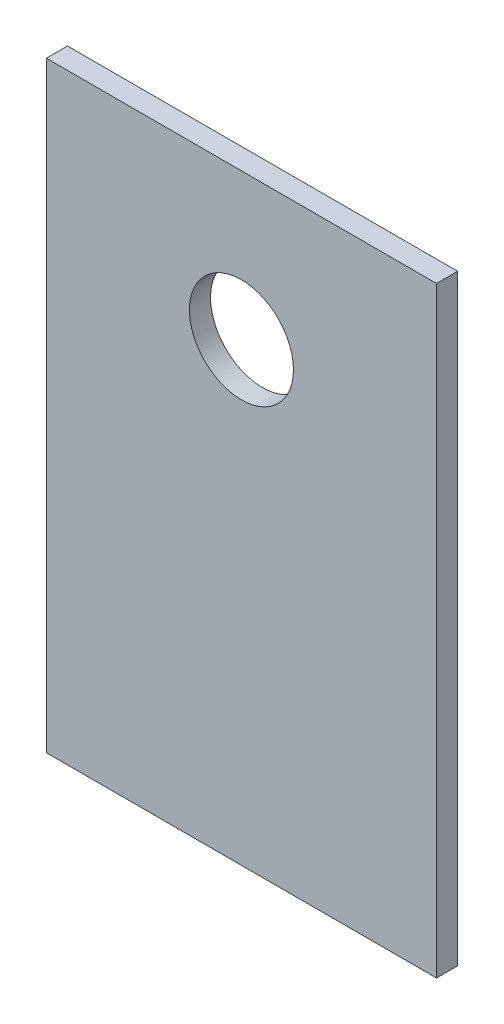
SolidWorks part; units mm, degrees
ref_plane "Front Plane" through (0, 0, 0) normal (0, 0, 1) x (1, 0, 0)
ref_plane "Top Plane" through (0, 0, 0) normal (0, 1, 0) x (1, 0, 0)
ref_plane "Right Plane" through (0, 0, 0) normal (1, 0, 0) x (0, 0, -1)
sketch "Sketch1" plane through (0, 0, 0) normal (0, 0, 1) x (1, 0, 0)
  line L0 (0, 0) -> (0, 4.5) construction
  line L1 (-6, -14) -> (6, -14)
  line L2 (-6, -14) -> (-6, 4.5)
  line L3 (-6, 4.5) -> (6, 4.5)
  line L4 (6, -14) -> (6, 4.5)
  circle A0 centre (0, 0) radius 1.6
  dimension "D1" = 3.2
  dimension "D2" = 12
  dimension "D3" = 18.5
  dimension "D4" = 4.5
extrude "Boss-Extrude1" add sketch "Sketch1" along normal blind 0.65
